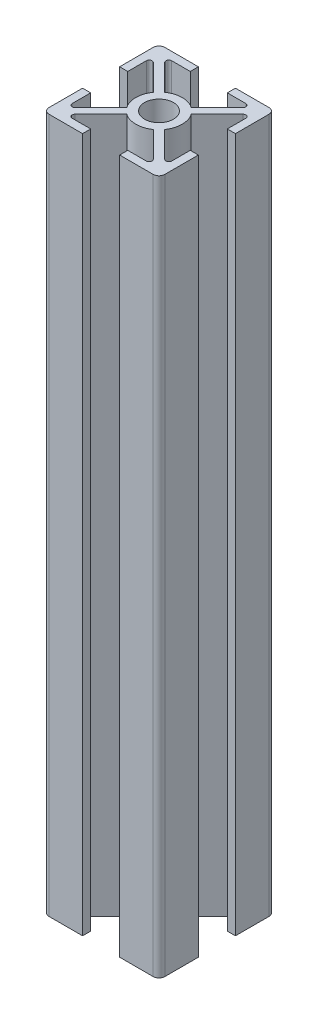
SolidWorks part; units mm, degrees
ref_plane "Front Plane" through (0, 0, 0) normal (0, 0, 1) x (1, 0, 0)
ref_plane "Top Plane" through (0, 0, 0) normal (0, 1, 0) x (1, 0, 0)
ref_plane "Right Plane" through (0, 0, 0) normal (1, 0, 0) x (0, 0, -1)
sketch "Sketch1" plane through (0, 0, 0) normal (0, 1, 0) x (1, 0, 0)
  line L0 (3.2, 10) -> (3.2, 8.6)
  line L1 (10, -3.2) -> (10, -10)
  line L2 (10, -3.2) -> (8.6, -3.2)
  line L3 (3.2, 10) -> (10, 10)
  line L4 (10, 3.2) -> (10, 10)
  line L5 (-10, -10) -> (10, 10) construction
  line L6 (-10, 10) -> (10, -10) construction
  line L7 (3.2, 8.6) -> (7.6101, 8.6)
  line L8 (7.6101, 8.6) -> (2.2898, 3.2798)
  line L9 (3.2798, 2.2898) -> (8.6, 7.6101)
  line L10 (8.6, 7.6101) -> (8.6, 3.2)
  line L11 (8.6, 3.2) -> (10, 3.2)
  line L12 (8.6, -3.2) -> (8.6, -7.6101)
  line L13 (8.6, -7.6101) -> (3.2798, -2.2898)
  line L14 (2.2898, -3.2798) -> (7.6101, -8.6)
  line L15 (7.6101, -8.6) -> (3.2, -8.6)
  line L16 (3.2, -10) -> (10, -10)
  line L17 (3.2, -8.6) -> (3.2, -10)
  line L18 (-3.2, -10) -> (-10, -10)
  line L19 (-3.2, -10) -> (-3.2, -8.6)
  line L20 (-3.2, -8.6) -> (-7.6101, -8.6)
  line L21 (-7.6101, -8.6) -> (-2.2898, -3.2798)
  line L22 (-3.2798, -2.2898) -> (-8.6, -7.6101)
  line L23 (-8.6, -7.6101) -> (-8.6, -3.2)
  line L24 (-10, -3.2) -> (-10, -10)
  line L25 (-8.6, -3.2) -> (-10, -3.2)
  line L26 (-10, 3.2) -> (-10, 10)
  line L27 (-10, 3.2) -> (-8.6, 3.2)
  line L28 (-8.6, 3.2) -> (-8.6, 7.6101)
  line L29 (-8.6, 7.6101) -> (-3.2798, 2.2898)
  line L30 (-2.2898, 3.2798) -> (-7.6101, 8.6)
  line L31 (-7.6101, 8.6) -> (-3.2, 8.6)
  line L32 (-3.2, 10) -> (-10, 10)
  line L33 (-3.2, 8.6) -> (-3.2, 10)
  circle A0 centre (0, 0) radius 2.5
  arc A1 (2.2898, 3.2798) -> (-2.2898, 3.2798) centre (0, 0) ccw
  arc A2 (-3.2798, 2.2898) -> (-3.2798, -2.2898) centre (0, 0) ccw
  arc A3 (-2.2898, -3.2798) -> (2.2898, -3.2798) centre (0, 0) ccw
  arc A4 (3.2798, -2.2898) -> (3.2798, 2.2898) centre (0, 0) ccw
  point P0 (0, 0)
  point P46 (0, 0)
  dimension "D3" = 5
  dimension "D4" = 8
  dimension "D1" = 20
  dimension "D2" = 20
  dimension "D5" = 6.8
  dimension "D6" = 6.8
  dimension "D7" = 1.4
  dimension "D8" = 0.7
  dimension "D9" = 1.4
  dimension "D10" = 4
extrude "Boss-Extrude1" add sketch "Sketch1" along normal blind 120
fillet "Fillet1" radius 0.5 8 edges at (7.6101, 60, -8.6) (8.6, 60, -7.6101) (8.6, 60, 7.6101) (7.6101, 60, 8.6) (-7.6101, 60, 8.6) (-8.6, 60, 7.6101) (-8.6, 60, -7.6101) (-7.6101, 60, -8.6)
fillet "Fillet2" radius 1 4 edges at (-10, 60, 10) (10, 60, 10) (10, 60, -10) (-10, 60, -10)
